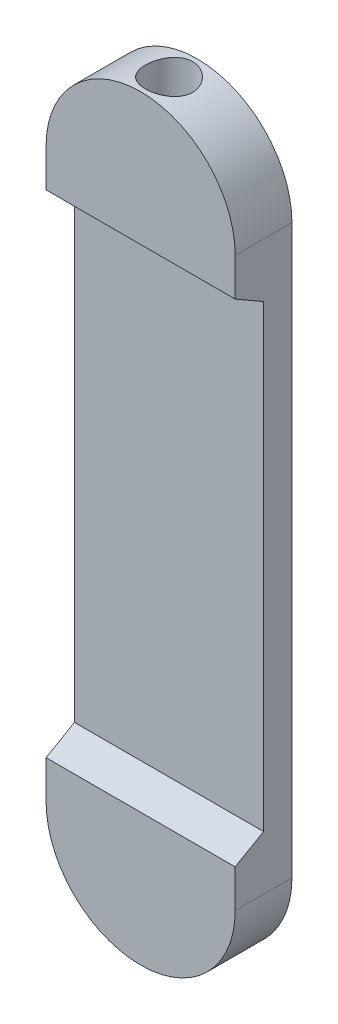
SolidWorks part; units mm, degrees
ref_plane "Front Plane" through (0, 0, 0) normal (0, 0, 1) x (1, 0, 0)
ref_plane "Top Plane" through (0, 0, 0) normal (0, 1, 0) x (1, 0, 0)
ref_plane "Right Plane" through (0, 0, 0) normal (1, 0, 0) x (0, 0, -1)
sketch "Sketch2" plane through (0, 0, 0) normal (0, 0, 1) x (1, 0, 0)
  line L2 (-50, -150) -> (-50, 150)
  line L4 (50, -150) -> (50, 150)
  line L5 (-50, -150) -> (50, 150) construction
  line L6 (-50, 150) -> (50, -150) construction
  arc A0 (50, 150) -> (-50, 150) centre (0, 150) ccw
  arc A1 (-50, -150) -> (50, -150) centre (0, -150) ccw
  point P0 (0, 0)
  dimension "D1" = 300
  dimension "D2" = 100
extrude "Boss-Extrude1" add sketch "Sketch2" along normal mid plane 30
ref_plane "Plane1" through (0, 150, 0) normal (0, 1, 0) x (1, 0, 0)
sketch "Sketch5" plane through (0, 150, 0) normal (0, 1, 0) x (1, 0, 0)
  circle A0 centre (0, 0) radius 12.5
  dimension "D1" = 25
extrude "Cut-Extrude1" cut sketch "Sketch5" along normal blind 59
ref_plane "Plane2" through (50, 0, 0) normal (1, 0, 0) x (0, 0, -1)
sketch "Sketch7" plane through (50, 0, 0) normal (1, 0, 0) x (0, 0, -1)
  line L0 (-15, 130) -> (0, 121.3397)
  line L1 (-15, -150) -> (-15, 150) construction
  line L2 (0, 121.3397) -> (0, -121.3397)
  line L3 (0, 0) -> (-15, 0) construction
  line L4 (16.5, 150) -> (-16.5, 150) construction
  line L5 (-15, -130) -> (0, -121.3397)
  line L6 (-15, 130) -> (-15, -130)
  dimension "D1" = 120
  dimension "D2" = 20
extrude "Cut-Extrude3" cut sketch "Sketch7" against normal blind 110
ref_plane "Plane3" through (0, -150, 0) normal (0, 1, 0) x (1, 0, 0)
sketch "Sketch10" plane through (0, -150, 0) normal (0, 1, 0) x (1, 0, 0)
  circle A0 centre (0, 0) radius 12.5
extrude "Cut-Extrude4" cut sketch "Sketch10" against normal blind 94
